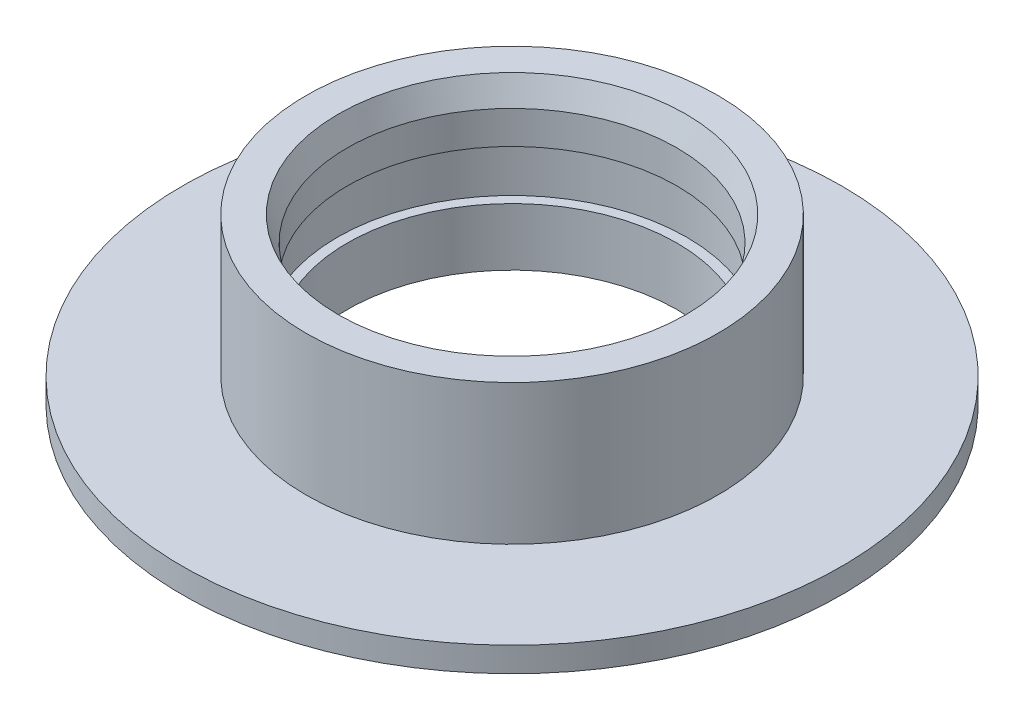
SolidWorks part; units mm, degrees
ref_plane "Plano frontal" through (0, 0, 0) normal (0, 0, 1) x (1, 0, 0)
ref_plane "Plano superior" through (0, 0, 0) normal (0, 1, 0) x (1, 0, 0)
ref_plane "Plano direito" through (0, 0, 0) normal (1, 0, 0) x (0, 0, -1)
sketch "Esboço1" plane through (0, 0, 0) normal (0, 0, 1) x (1, 0, 0)
  line L0 (0, 0) -> (0, 131.4233) construction
  line L1 (0, 0) -> (201.1168, 0) construction
  line L2 (100, 0) -> (100, 35)
  line L3 (100, 85) -> (105.4596, 100)
  line L4 (105.4596, 100) -> (125, 100)
  line L5 (125, 100) -> (125, 15)
  line L6 (125, 15) -> (200, 15)
  line L7 (200, 15) -> (200, 0)
  line L8 (200, 0) -> (100, 0)
  line L9 (100, 65) -> (106, 65)
  line L10 (106, 65) -> (106, 35)
  line L11 (106, 35) -> (100, 35)
  line L12 (100, 65) -> (100, 85)
  dimension "D1" = 100
  dimension "D2" = 15
  dimension "D3" = 250
  dimension "D4" = 200
  dimension "D5" = 20
  dimension "D6" = 15
  dimension "D7" = 20
  dimension "D8" = 6
  dimension "D9" = 30
  dimension "D10" = 400
revolve "Revolução1" add sketch "Esboço1" angle 360 about L0
